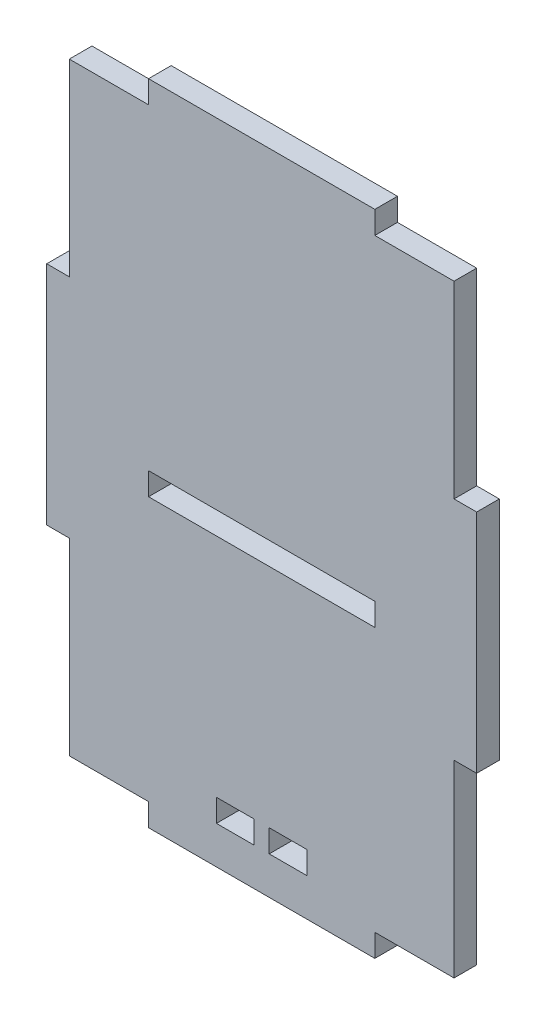
SolidWorks part; units mm, degrees
ref_plane "Front Plane" through (0, 0, 0) normal (0, 0, 1) x (1, 0, 0)
ref_plane "Top Plane" through (0, 0, 0) normal (0, 1, 0) x (1, 0, 0)
ref_plane "Right Plane" through (0, 0, 0) normal (1, 0, 0) x (0, 0, -1)
sketch "Sketch1" plane through (0, 0, 0) normal (0, 0, 1) x (1, 0, 0)
  line L0 (-25.5, -15) -> (-25.5, -40)
  line L1 (-25.5, 40) -> (-15, 40)
  line L2 (-25.5, 40) -> (-25.5, 15)
  line L3 (-25.5, -40) -> (-15, -40)
  line L4 (25.5, 40) -> (25.5, 15)
  line L5 (-25.5, 40) -> (25.5, -40) construction
  line L6 (-25.5, -40) -> (25.5, 40) construction
  line L7 (-15, -2) -> (15, -2)
  line L8 (-15, -2) -> (-15, -5)
  line L9 (-15, -5) -> (15, -5)
  line L10 (15, -2) -> (15, -5)
  line L11 (1, -38) -> (6, -38)
  line L12 (1, -38) -> (1, -35)
  line L13 (1, -35) -> (6, -35)
  line L14 (6, -38) -> (6, -35)
  line L15 (-1, -35) -> (-6, -35)
  line L16 (-1, -35) -> (-1, -38)
  line L17 (-1, -38) -> (-6, -38)
  line L18 (-6, -35) -> (-6, -38)
  line L19 (-25.5, 15) -> (-28.5, 15)
  line L20 (15, 40) -> (25.5, 40)
  line L21 (-25.5, -15) -> (-28.5, -15)
  line L22 (-28.5, 15) -> (-28.5, -15)
  line L23 (25.5, 15) -> (28.5, 15)
  line L24 (15, -40) -> (25.5, -40)
  line L25 (25.5, -15) -> (28.5, -15)
  line L26 (28.5, 15) -> (28.5, -15)
  line L27 (25.5, -15) -> (25.5, -40)
  line L28 (-15, 40) -> (-15, 43)
  line L29 (-15, 43) -> (15, 43)
  line L30 (15, 40) -> (15, 43)
  line L32 (-15, -40) -> (-15, -43)
  line L33 (-15, -43) -> (15, -43)
  line L34 (15, -40) -> (15, -43)
  point P0 (0, 0)
  dimension "D1" = 51
  dimension "D2" = 80
  dimension "D3" = 35
  dimension "D4" = 30
  dimension "D5" = 3
  dimension "D6" = 10.5
  dimension "D7" = 2
  dimension "D8" = 2
  dimension "D9" = 5
  dimension "D10" = 5
  dimension "D11" = 19.5
  dimension "D12" = 19.5
  dimension "D13" = 3
  dimension "D14" = 3
  dimension "D15" = 3
  dimension "D16" = 3
  dimension "D17" = 30
  dimension "D18" = 30
  dimension "D19" = 25
  dimension "D20" = 25
  dimension "D21" = 3
  dimension "D22" = 30
  dimension "D23" = 30
  dimension "1.2" = 10.5
  dimension "D24" = 10.5
  dimension "D25" = 3
extrude "Boss-Extrude1" add sketch "Sketch1" along normal mid plane 3
